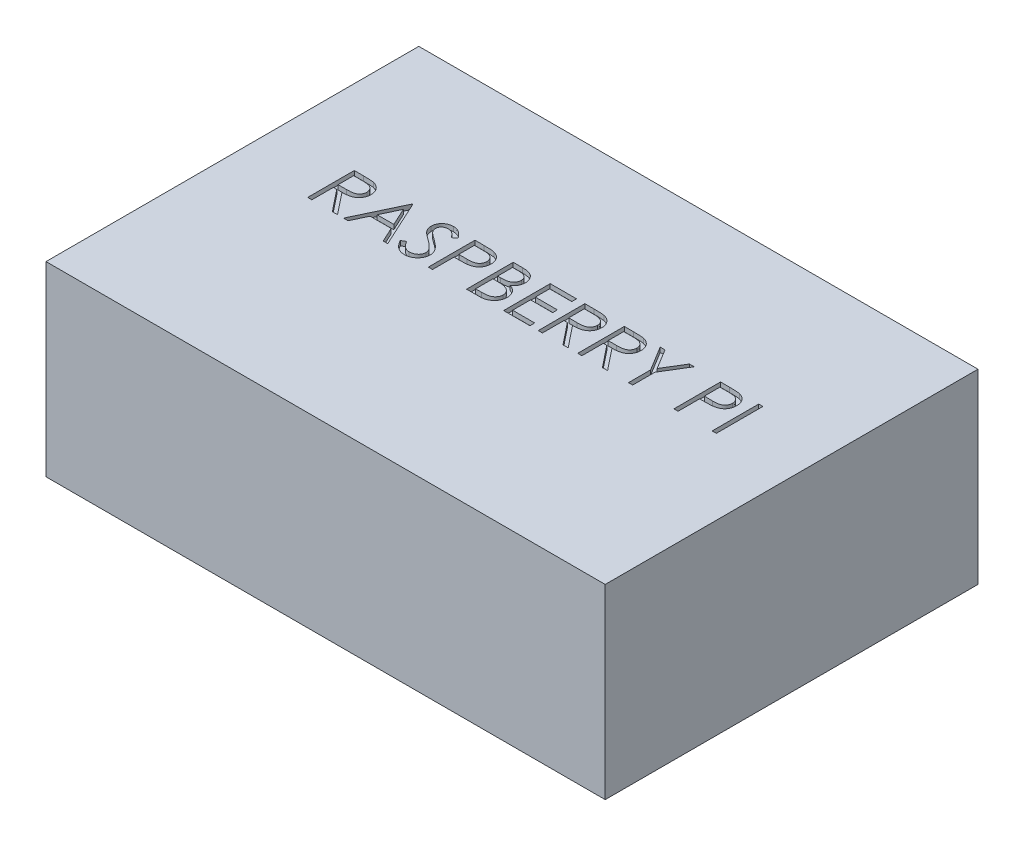
SolidWorks part; units mm, degrees
ref_plane "Front Plane" through (0, 0, 0) normal (0, 0, 1) x (1, 0, 0)
ref_plane "Top Plane" through (0, 0, 0) normal (0, 1, 0) x (1, 0, 0)
ref_plane "Right Plane" through (0, 0, 0) normal (1, 0, 0) x (0, 0, -1)
sketch "Sketch1" plane through (0, 0, 0) normal (0, 1, 0) x (1, 0, 0)
  line L1 (0, 0) -> (120, 0)
  line L2 (0, 0) -> (0, 80)
  line L3 (0, 80) -> (120, 80)
  line L4 (120, 0) -> (120, 80)
  dimension "D1" = 80
  dimension "D2" = 120
extrude "Boss-Extrude1" add sketch "Sketch1" along normal blind 40
sketch "Sketch2" plane through (0, 40, 0) normal (0, 1, 0) x (1, 0, 0)
  line L0 (0, 40) -> (120, 40) construction
  line L1 (0, 80) -> (0, 0) construction
  line L2 (120, 0) -> (120, 80) construction
  text T0 "RASPBERRY PI" font "Century Gothic" height 10
extrude "Cut-Extrude1" cut sketch "Sketch2" against normal blind 1
